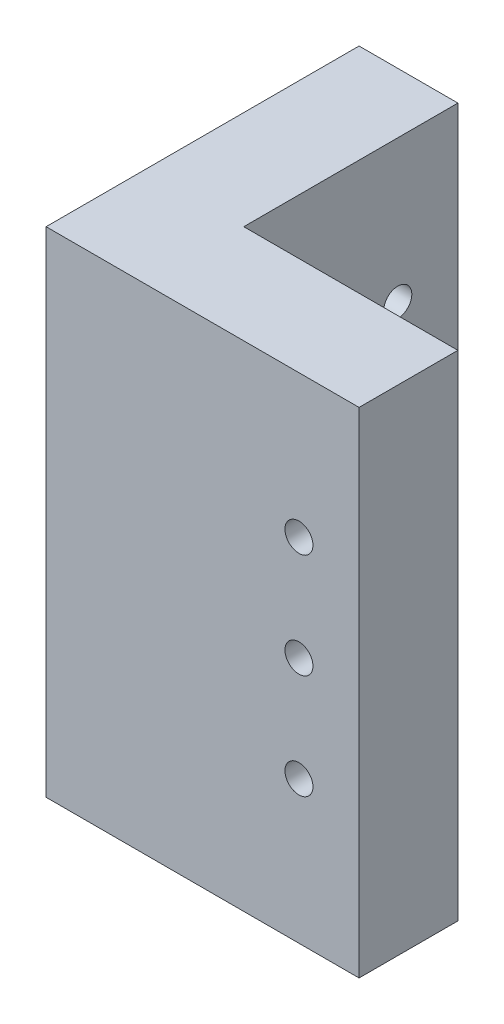
SolidWorks part; units mm, degrees
ref_plane "Front" through (0, 0, 0) normal (0, 0, 1) x (1, 0, 0)
ref_plane "Top" through (0, 0, 0) normal (0, 1, 0) x (1, 0, 0)
ref_plane "Right" through (0, 0, 0) normal (1, 0, 0) x (0, 0, -1)
sketch "Sketch1" plane through (0, 0, 0) normal (0, 1, 0) x (1, 0, 0)
  line L0 (-3, 10) -> (-3, -3)
  line L9 (0, 0) -> (10, 0) construction
  line L10 (0, 0) -> (0, 10) construction
  line L11 (0, 10) -> (10, 10) construction
  line L12 (10, 0) -> (10, 10) construction
  line L13 (10, 10) -> (-3, 10) construction
  line L14 (10, 10) -> (10, -3) construction
  line L15 (10, -3) -> (-3, -3) construction
  line L16 (-3, 10) -> (-3, -3) construction
  line L17 (-3, -3) -> (10, -3)
  line L18 (10, -3) -> (10, -9)
  line L19 (10, -9) -> (-9, -9)
  line L20 (-9, -9) -> (-9, 10)
  line L21 (-9, 10) -> (-3, 10)
  dimension "D1" = 10
  dimension "D2" = 3
  dimension "D3" = 6
extrude "Boss-Extrude1" add sketch "Sketch1" along normal mid plane 30
ref_plane "Plane1" through (0, 0, 0) normal (0.7071, 0, 0.7071) x (0.7071, 0, -0.7071)
sketch "Sketch2" plane through (0, 0, 9) normal (0, 0, 1) x (1, 0, 0)
  line L0 (0, 0) -> (6.35, 0) construction
  line L2 (6.35, -6.35) -> (6.35, 6.35) construction
  circle A0 centre (6.35, 6.35) radius 0.85
  circle A1 centre (6.35, 0) radius 0.85
  circle A2 centre (6.35, -6.35) radius 0.85
  point P5 (6.35, 0)
  dimension "D3" = 1.7
  dimension "D1" = 6.35
  dimension "D2" = 12.7
extrude "Cut-Extrude1" cut sketch "Sketch2" against normal through all
mirror "Mirror1" about plane through (0, 0, 0) normal (0.7071, 0, 0.7071) of "Cut-Extrude1"
